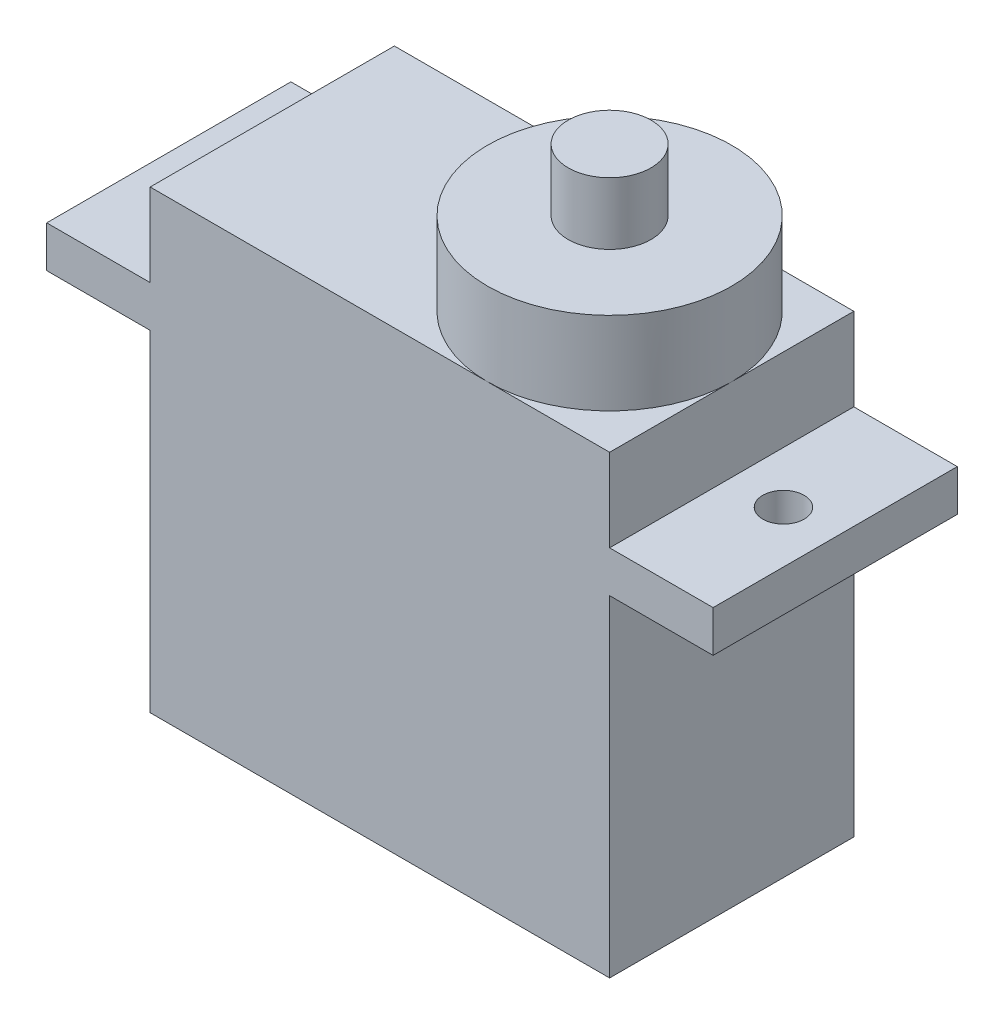
SolidWorks part; units mm, degrees
ref_plane "Plan de face" through (0, 0, 0) normal (0, 0, 1) x (1, 0, 0)
ref_plane "Plan de dessus" through (0, 0, 0) normal (0, 1, 0) x (1, 0, 0)
ref_plane "Plan de droite" through (0, 0, 0) normal (1, 0, 0) x (0, 0, -1)
sketch "Esquisse1" plane through (0, 0, 0) normal (0, 0, 1) x (1, 0, 0)
  line L0 (-45.1965, 18) -> (-40.1965, 18)
  line L1 (-40.1965, 18) -> (-40.1965, 22)
  line L2 (-40.1965, 22) -> (-17.9965, 22)
  line L3 (-17.9965, 22) -> (-17.9965, 18)
  line L4 (-17.9965, 18) -> (-12.9965, 18)
  line L5 (-12.9965, 18) -> (-12.9965, 16)
  line L6 (-12.9965, 16) -> (-17.9965, 16)
  line L7 (-17.9965, 16) -> (-17.9965, 0)
  line L8 (-17.9965, 0) -> (-40.1965, 0)
  line L9 (-40.1965, 0) -> (-40.1965, 16)
  line L10 (-40.1965, 16) -> (-45.1965, 16)
  line L11 (-45.1965, 16) -> (-45.1965, 18)
  dimension "D1" = 22.2
  dimension "D2" = 22.2
  dimension "D3" = 32.2
  dimension "D4" = 5
  dimension "D5" = 16
  dimension "D6" = 2
  dimension "D7" = 16
  dimension "D8" = 2
  dimension "D9" = 4
extrude "Boss.-Extru.1" add sketch "Esquisse1" along normal blind 11.8
sketch "Esquisse2" plane through (0, 18, 0) normal (0, 1, 0) x (1, 0, 0)
  line L0 (-40.1965, -11.8) -> (-40.1965, 0) construction
  line L1 (-17.9965, 0) -> (-40.1965, 0) construction
  line L2 (-12.9965, 0) -> (-17.9965, 0) construction
  line L3 (-17.9965, -11.8) -> (-17.9965, 0) construction
  circle A0 centre (-42.6965, -5.9) radius 1
  circle A1 centre (-15.4965, -5.9) radius 1
  dimension "D1" = 2.5
  dimension "D2" = 2
  dimension "D3" = 5.9
  dimension "D4" = 5.9
  dimension "D5" = 2.5
  dimension "D6" = 2
extrude "Enlèv. mat.-Extru.1" cut sketch "Esquisse2" against normal blind 11.8
sketch "Esquisse3" plane through (0, 22, 0) normal (0, 1, 0) x (1, 0, 0)
  line L0 (-17.9965, 0) -> (-40.1965, 0) construction
  line L1 (-17.9965, -11.8) -> (-17.9965, 0) construction
  circle A0 centre (-23.8965, -5.9) radius 5.9
  dimension "D1" = 11.8
  dimension "D2" = 5.9
  dimension "D3" = 5.9
extrude "Boss.-Extru.2" add sketch "Esquisse3" along normal blind 4
sketch "Esquisse4" plane through (0, 26, 0) normal (0, 1, 0) x (1, 0, 0)
  line L0 (-23.8965, 0) -> (-40.1965, 0) construction
  line L1 (-17.9965, -11.8) -> (-17.9965, 0) construction
  circle A0 centre (-23.8965, -5.9) radius 2
  dimension "D1" = 4
  dimension "D2" = 5.9
  dimension "D3" = 5.9
extrude "Boss.-Extru.3" add sketch "Esquisse4" along normal blind 3
sketch "Esquisse5" plane through (-17.9965, 0, 0) normal (1, 0, 0) x (0, 0, -1)
  line L0 (-11.8, 0) -> (-11.8, 16) construction
  line L1 (-8.3, 3) -> (-3.3, 3)
  line L2 (-8.3, 3) -> (-8.3, 7)
  line L3 (-8.3, 7) -> (-3.3, 7)
  line L4 (-3.3, 3) -> (-3.3, 7)
  line L5 (-11.8, 0) -> (0, 0) construction
  dimension "D1" = 5
  dimension "D2" = 3.5
  dimension "D3" = 4
  dimension "D4" = 3
extrude "Boss.-Extru.4" add sketch "Esquisse5" along normal blind 3
sketch "Esquisse6" plane through (0, 7, 0) normal (0, 1, 0) x (1, 0, 0)
  line L1 (-17.9965, -8.3) -> (-14.9965, -8.3)
  line L2 (-17.9965, -8.3) -> (-17.9965, -3.3)
  line L3 (-17.9965, -3.3) -> (-14.9965, -3.3)
  line L4 (-14.9965, -8.3) -> (-14.9965, -3.3)
extrude "Enlèv. mat.-Extru.2" cut sketch "Esquisse6" against normal blind 10
